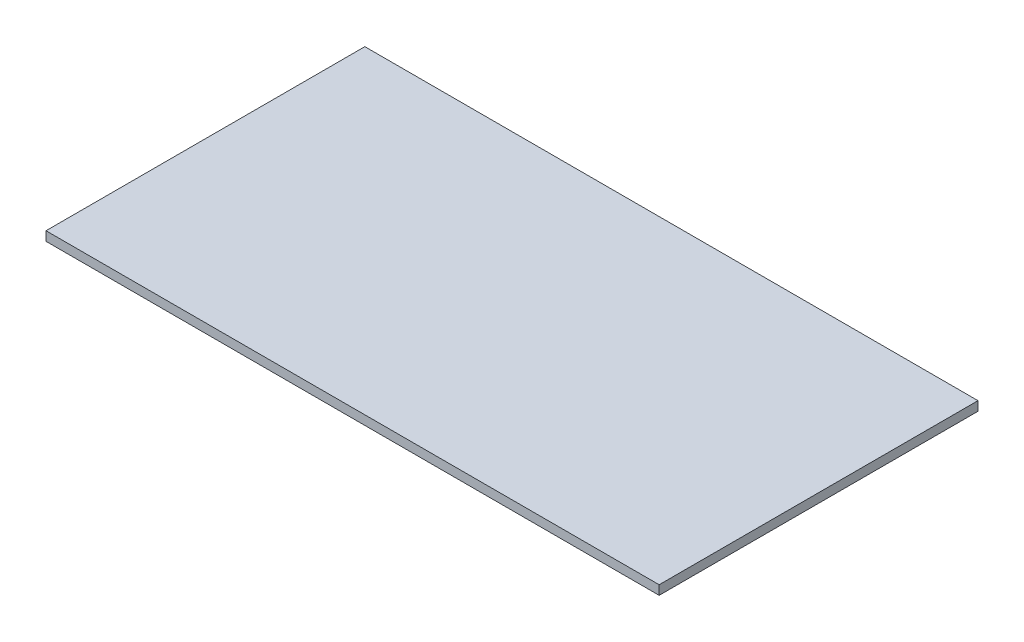
SolidWorks part; units mm, degrees
ref_plane "Front Plane" through (0, 0, 0) normal (0, 0, 1) x (1, 0, 0)
ref_plane "Top Plane" through (0, 0, 0) normal (0, 1, 0) x (1, 0, 0)
ref_plane "Right Plane" through (0, 0, 0) normal (1, 0, 0) x (0, 0, -1)
sketch "Sketch1" plane through (0, 0, 0) normal (0, 1, 0) x (1, 0, 0)
  line L1 (-635, -330.2) -> (635, -330.2)
  line L2 (-635, -330.2) -> (-635, 330.2)
  line L3 (-635, 330.2) -> (635, 330.2)
  line L4 (635, -330.2) -> (635, 330.2)
  line L5 (-635, -330.2) -> (635, 330.2) construction
  line L6 (-635, 330.2) -> (635, -330.2) construction
  point P0 (0, 0)
  dimension "D1" = 660.4
  dimension "D2" = 1270
extrude "Boss-Extrude1" add sketch "Sketch1" along normal blind 19.05
